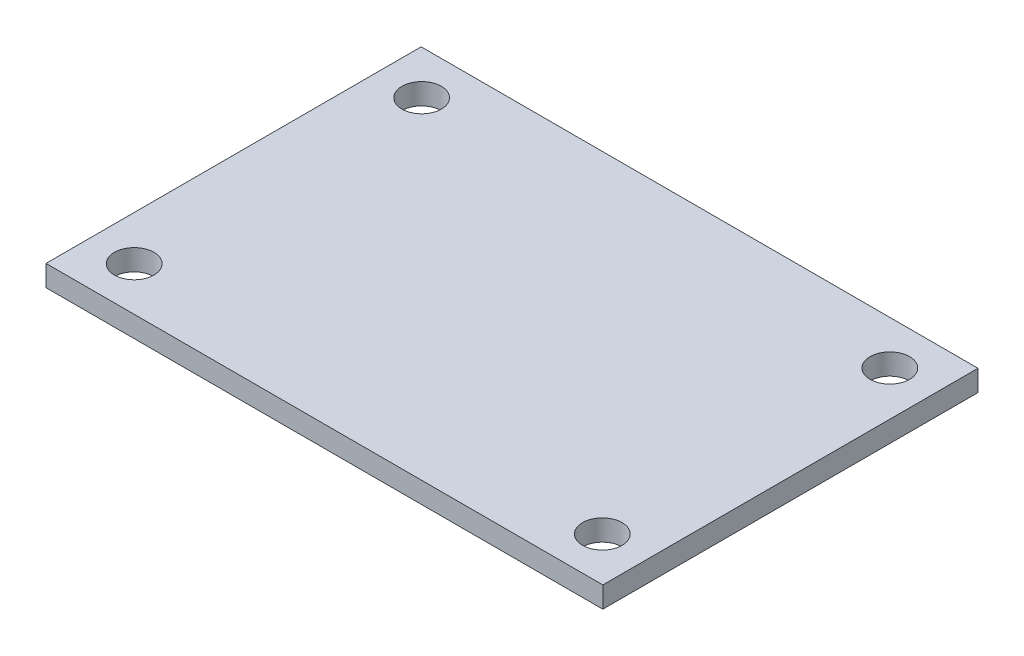
SolidWorks part; units mm, degrees
ref_plane "Front Plane" through (0, 0, 0) normal (0, 0, 1) x (1, 0, 0)
ref_plane "Top Plane" through (0, 0, 0) normal (0, 1, 0) x (1, 0, 0)
ref_plane "Right Plane" through (0, 0, 0) normal (1, 0, 0) x (0, 0, -1)
sketch "Sketch1" plane through (0, 0, 0) normal (0, 1, 0) x (1, 0, 0)
  line L0 (21.15, 0) -> (-21.15, 0) construction
  line L1 (21.15, -14.25) -> (-21.15, -14.25)
  line L2 (21.15, -14.25) -> (21.15, 14.25)
  line L3 (21.15, 14.25) -> (-21.15, 14.25)
  line L4 (-21.15, -14.25) -> (-21.15, 14.25)
  line L5 (21.15, -14.25) -> (-21.15, 14.25) construction
  line L6 (21.15, 14.25) -> (-21.15, -14.25) construction
  line L7 (0, -14.25) -> (0, 14.25) construction
  circle A0 centre (-17.7817, 10.9198) radius 1.5
  circle A1 centre (17.7817, 10.9198) radius 1.5
  circle A2 centre (17.7817, -10.9198) radius 1.5
  circle A3 centre (-17.7817, -10.9198) radius 1.5
  point P0 (0, 0)
  point P11 (0, 0)
  point P14 (0, 0)
  dimension "D3" = 3
  dimension "D1" = 42.3
  dimension "D2" = 28.5
  dimension "D4" = 3.3302
  dimension "D5" = 3.3683
extrude "Boss-Extrude1" add sketch "Sketch1" along normal blind 1.6
